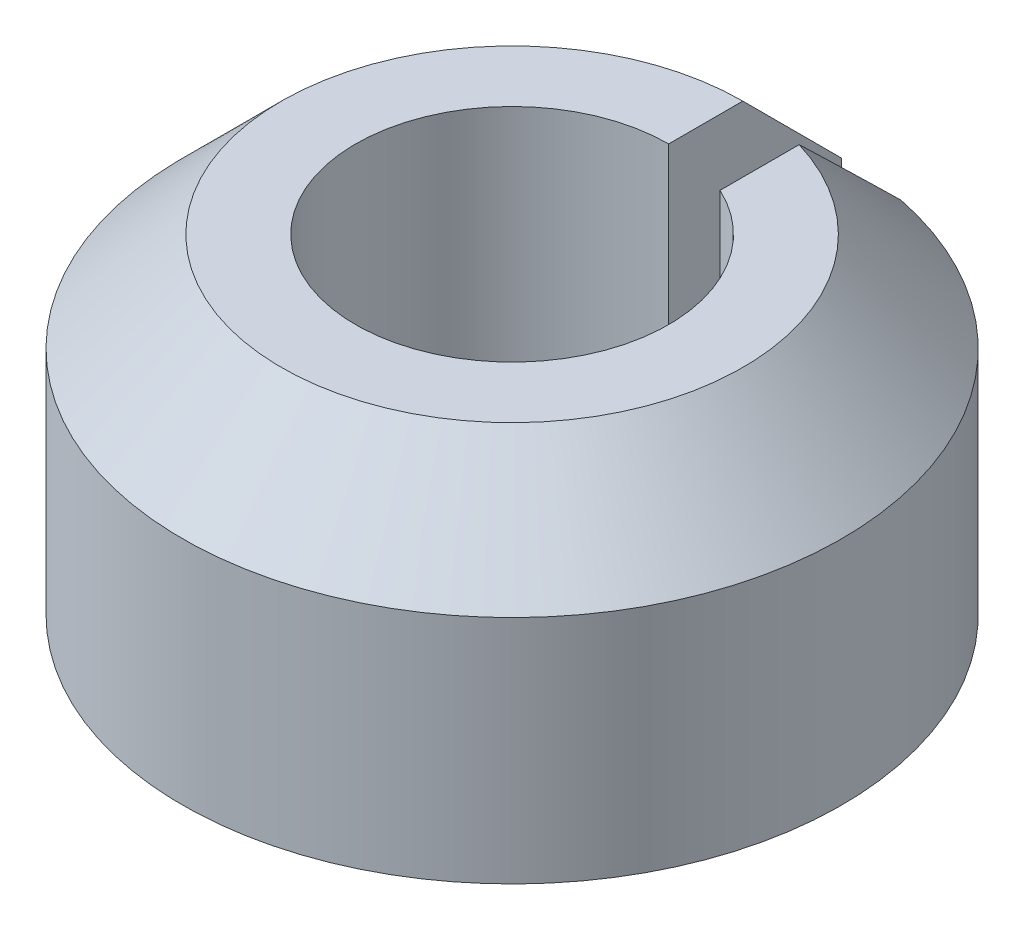
SolidWorks part; units mm, degrees
ref_plane "Спереди" through (0, 0, 0) normal (0, 0, 1) x (1, 0, 0)
ref_plane "Сверху" through (0, 0, 0) normal (0, 1, 0) x (1, 0, 0)
ref_plane "Справа" through (0, 0, 0) normal (1, 0, 0) x (0, 0, -1)
sketch "Эскиз1" plane through (0, 0, 0) normal (0, 1, 0) x (1, 0, 0)
  line L0 (0, 0.95) -> (0, 2)
  line L1 (0.4, 1.9596) -> (0.4, 0.8617)
  arc A0 (0, 2) -> (0.4, 1.9596) centre (0, 0) ccw
  arc A1 (0, 0.95) -> (0.4, 0.8617) centre (0, 0) ccw
  dimension "D1" = 0.4
  dimension "D2" = 2
extrude "Бобышка-Вытянуть1" add sketch "Эскиз1" along normal blind 2
chamfer "Фаска1" distance 0.6 angle 45 1 edges at (-0.201, 2, 1.9899)
